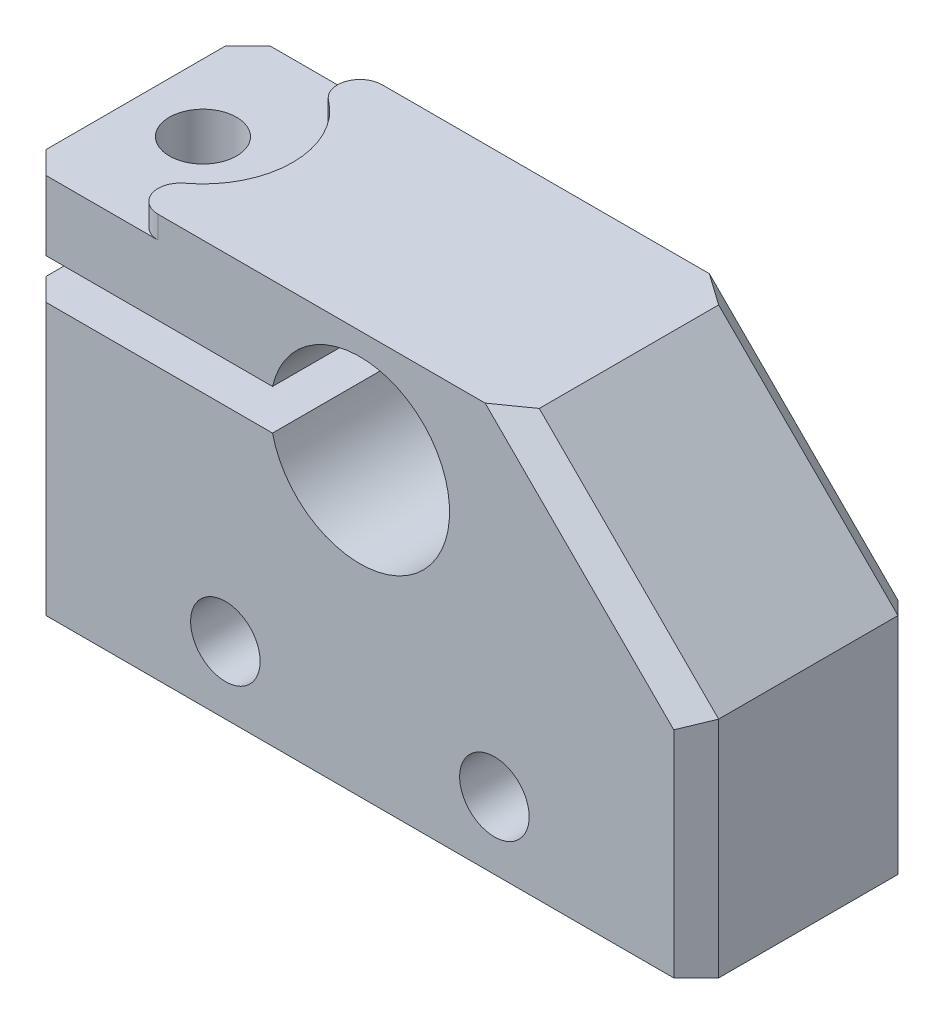
SolidWorks part; units mm, degrees
ref_plane "Front Plane" through (0, 0, 0) normal (0, 0, 1) x (1, 0, 0)
ref_plane "Top Plane" through (0, 0, 0) normal (0, 1, 0) x (1, 0, 0)
ref_plane "Right Plane" through (0, 0, 0) normal (1, 0, 0) x (0, 0, -1)
sketch "Sketch3" plane through (0, 0, 0) normal (0, 0, 1) x (1, 0, 0)
  line L0 (0, 4) -> (0, -4) construction
  line L1 (-15, -4) -> (15, -4)
  line L2 (-15, -4) -> (-15, 4)
  line L3 (-15, 4) -> (15, 4)
  line L4 (15, -4) -> (15, 4)
  line L5 (-15, -4) -> (15, 4) construction
  line L6 (-15, 4) -> (15, -4) construction
  circle A0 centre (-6, -1) radius 1.55
  circle A1 centre (6, -1) radius 1.55
  point P0 (0, 0)
  point P12 (0, -6.1655)
  point P13 (5.3676, 0)
  point P14 (-6, 0)
  point P15 (0, -4)
  dimension "D1" = 12
  dimension "D5" = 3.1
  dimension "D2" = 3
  dimension "D3" = 8
  dimension "D4" = 30
extrude "Boss-Extrude1" add sketch "Sketch3" along normal mid plane 10
sketch "Sketch6" plane through (0, 0, 5) normal (0, 0, 1) x (1, 0, 0)
  line L0 (-15, 4) -> (15, 4)
  line L2 (7, 14) -> (-15, 14)
  line L3 (-15, 14) -> (-15, 4)
  line L4 (0, 14) -> (0, 0) construction
  line L5 (15, 4) -> (15, 6)
  line L6 (15, 6) -> (7, 14)
  circle A0 centre (0, 9) radius 4
  point P8 (0, 0)
  point P9 (0, 8.3012)
  point P13 (0, 8.3407)
  dimension "D1" = 8
  dimension "D2" = 5
  dimension "D5" = 5
  dimension "D3" = 8
  dimension "D4" = 45
extrude "Boss-Extrude2" add sketch "Sketch6" against normal up to surface (10 mm away) up to face at (-4.45, -1, -5)
sketch "Sketch8" plane through (0, 0, 5) normal (0, 0, 1) x (1, 0, 0)
  line L0 (0, 9) -> (-15, 9)
  line L1 (-15, 14) -> (-15, -4) construction
extrude "Cut-Extrude-Thin1" cut sketch "Sketch8" against normal through all both and the other way through all thin thin type mid plane wall 1.8
sketch "Sketch9" plane through (0, 14, 0) normal (0, 1, 0) x (1, 0, 0)
  line L0 (-15, 5) -> (-15, -5) construction
  circle A0 centre (-12, 0) radius 1.5
  dimension "D1" = 3
  dimension "D2" = 3
extrude "Cut-Extrude1" cut sketch "Sketch9" against normal through all
sketch "Sketch10" plane through (0, 14, 0) normal (0, 1, 0) x (1, 0, 0)
  line L5 (7, 5) -> (-15, 5) construction
  line L6 (7, -5) -> (-15, -5) construction
  line L7 (-9, 5) -> (-15, 5)
  line L8 (-15, 5) -> (-15, -5)
  line L9 (-15, -5) -> (-9, -5)
  arc A0 (-9, 5) -> (-9.6, 3.2) centre (-9, 4) ccw
  arc A1 (-9.6, 3.2) -> (-9.6, -3.2) centre (-12, 0) cw
  arc A2 (-9.6, -3.2) -> (-9, -5) centre (-9, -4) ccw
  point P8 (0, 0)
  point P10 (-12.5765, 0)
  point P12 (-11.263, 0)
  point P13 (-12, 0)
  point P17 (-13.5, 0)
  dimension "D1" = 6
  dimension "D2" = 1
extrude "Cut-Extrude2" cut sketch "Sketch10" against normal blind 1
chamfer "Chamfer2" distance 1 angle 45 8 edges at (-15, 2.05, -5) (-15, 11.45, -5) (-15, 11.45, 5) (-15, 2.05, 5) (15, 1, -5) (11, 10, -5) (11, 10, 5) (15, 1, 5)
